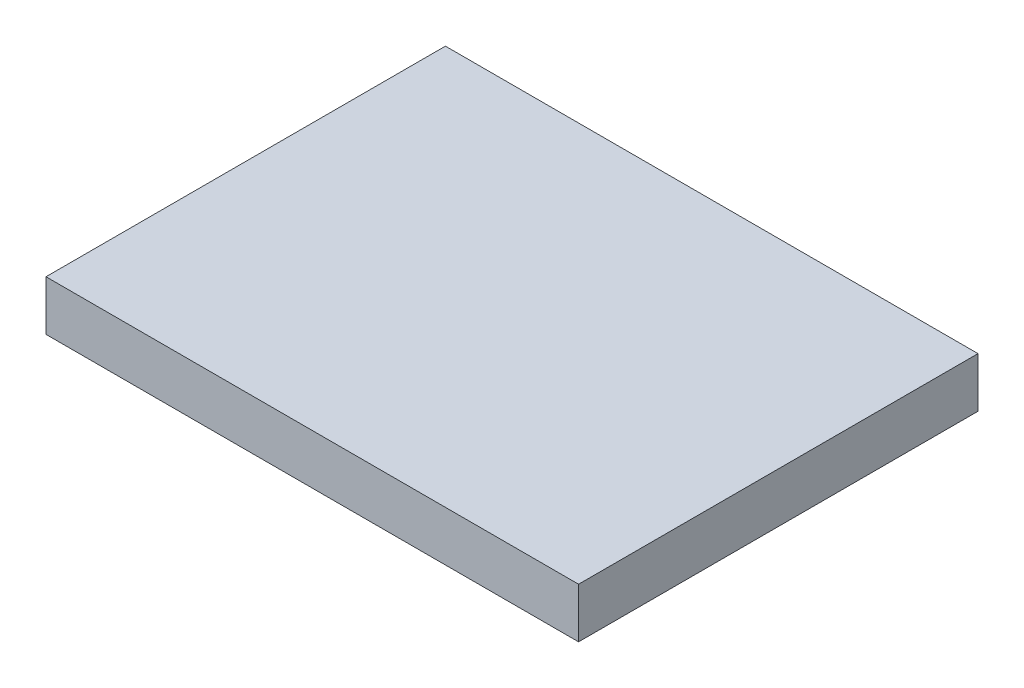
SolidWorks part; units mm, degrees
material "Foam#1"
ref_plane "Front Plane" through (0, 0, 0) normal (0, 0, 1) x (1, 0, 0)
ref_plane "Top Plane" through (0, 0, 0) normal (0, 1, 0) x (1, 0, 0)
ref_plane "Right Plane" through (0, 0, 0) normal (1, 0, 0) x (0, 0, -1)
sketch "Sketch1" plane through (0, 0, 0) normal (0, 1, 0) x (1, 0, 0)
  line L1 (-25.4, -19.05) -> (25.4, -19.05)
  line L2 (-25.4, -19.05) -> (-25.4, 19.05)
  line L3 (-25.4, 19.05) -> (25.4, 19.05)
  line L4 (25.4, -19.05) -> (25.4, 19.05)
  line L5 (-25.4, -19.05) -> (25.4, 19.05) construction
  line L6 (-25.4, 19.05) -> (25.4, -19.05) construction
  point P0 (0, 0)
  dimension "D1" = 50.8
  dimension "D2" = 38.1
extrude "Boss-Extrude1" add sketch "Sketch1" along normal blind 4.7625
